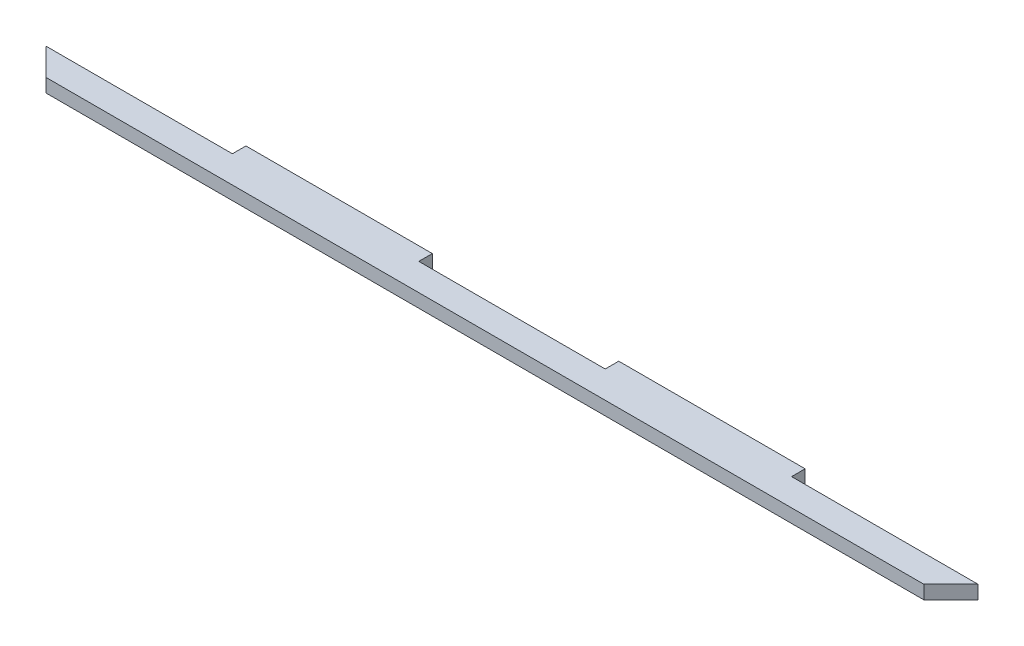
SolidWorks part; units mm, degrees
ref_plane "Front Plane" through (0, 0, 0) normal (0, 0, 1) x (1, 0, 0)
ref_plane "Top Plane" through (0, 0, 0) normal (0, 1, 0) x (1, 0, 0)
ref_plane "Right Plane" through (0, 0, 0) normal (1, 0, 0) x (0, 0, -1)
sketch "Sketch1" plane through (0, 0, 0) normal (0, 1, 0) x (1, 0, 0)
  line L0 (-61.95, 4.5) -> (-20.65, 4.5)
  line L3 (-97.25, -4.5) -> (97.25, -4.5)
  line L5 (61.95, 1.5) -> (103.25, 1.5)
  line L6 (-20.65, 1.5) -> (20.65, 1.5)
  line L8 (20.65, 4.5) -> (61.95, 4.5)
  line L10 (-61.95, 4.5) -> (-61.95, 1.5)
  line L11 (-103.25, 1.5) -> (-61.95, 1.5)
  line L12 (-20.65, 4.5) -> (-20.65, 1.5)
  line L13 (20.65, 4.5) -> (20.65, 1.5)
  line L14 (61.95, 4.5) -> (61.95, 1.5)
  line L15 (-103.25, 1.5) -> (-97.25, -4.5)
  line L16 (103.25, 1.5) -> (97.25, -4.5)
  point P0 (0, 0)
extrude "Boss-Extrude1" add sketch "Sketch1" along normal blind 3
